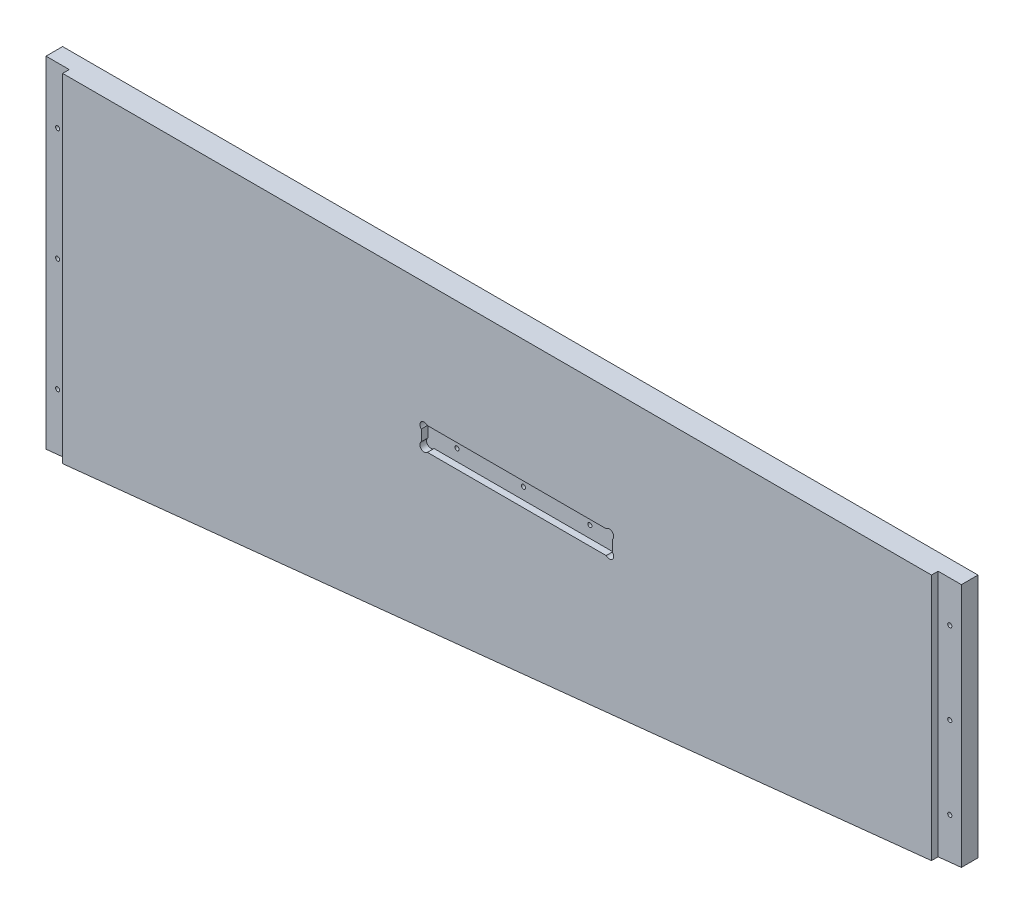
SolidWorks part; units mm, degrees
material "Pine"
ref_plane "Front Plane" through (0, 0, 0) normal (0, 0, 1) x (1, 0, 0)
ref_plane "Top Plane" through (0, 0, 0) normal (0, 1, 0) x (1, 0, 0)
ref_plane "Right Plane" through (0, 0, 0) normal (1, 0, 0) x (0, 0, -1)
sketch "Sketch1" plane through (0, 0, 0) normal (0, 0, 1) x (1, 0, 0)
  line L0 (-163.9887, -5335.905) -> (-163.9887, -5432.425)
  line L1 (-102.87, -5350.891) -> (-33.02, -5350.891)
  line L2 (-111.8235, -5341.9375) -> (-111.8235, -5334)
  line L3 (-24.0665, -5341.9375) -> (-24.0665, -5334)
  line L4 (-298.9262, -5332.73) -> (-167.1637, -5332.73)
  line L5 (-167.1637, -5435.6) -> (-298.9262, -5435.6)
  line L6 (-302.1012, -5432.425) -> (-302.1012, -5335.905)
  line L7 (-107.6325, -5329.809) -> (-28.2575, -5329.809)
  line L8 (174.9425, -5308.6) -> (174.9425, -5581.65)
  line L9 (449.2625, -5413.1661) -> (449.2625, -5421.9659)
  line L10 (595.3125, -5421.9659) -> (595.3125, -5413.1661)
  line L11 (839.47, -5509.5521) -> (839.47, -5307.6729)
  line L12 (839.47, -5307.6729) -> (863.6, -5307.6729)
  line L13 (839.47, -5509.5521) -> (863.6, -5509.5521)
  line L14 (863.6, -5509.5521) -> (863.6, -5307.6729)
  line L15 (-354.2665, -5341.9375) -> (-354.2665, -5334)
  line L16 (-100.8856, -5889.625) -> (-50.0856, -5889.625)
  line L17 (-104.0606, -5969) -> (-104.0606, -5892.8)
  line L18 (-46.9106, -5892.8) -> (-46.9106, -5969)
  line L19 (-50.0856, -5972.175) -> (-100.8856, -5972.175)
  line L20 (-100.8856, -5848.35) -> (-50.0856, -5848.35)
  line L21 (857.25, -5502.275) -> (157.1625, -5575.3)
  line L22 (857.25, -5314.95) -> (857.25, -5502.275)
  line L23 (157.1625, -5314.95) -> (157.1625, -5575.3)
  line L24 (857.25, -5314.95) -> (157.1625, -5314.95)
  line L25 (150.8125, -5308.6) -> (174.9425, -5308.6)
  line L26 (174.9425, -5581.65) -> (150.8125, -5581.65)
  line L27 (137.16, -5314.95) -> (137.16, -5502.275)
  line L28 (150.8125, -5581.65) -> (150.8125, -5308.6)
  line L29 (590.8224, -5408.676) -> (453.7526, -5408.676)
  line L30 (453.7526, -5426.456) -> (590.8224, -5426.456)
  line L31 (137.16, -6013.45) -> (137.16, -5867.4)
  line L32 (150.8125, -5746.75) -> (150.8125, -6019.8)
  line L33 (143.51, -5639.9938) -> (143.51, -5654.294)
  line L34 (590.8224, -5919.724) -> (453.7526, -5919.724)
  line L35 (453.7526, -5901.944) -> (590.8224, -5901.944)
  line L36 (449.2625, -5915.2339) -> (449.2625, -5906.4341)
  line L37 (174.9425, -6019.8) -> (174.9425, -5746.75)
  line L38 (595.3125, -5906.4341) -> (595.3125, -5915.2339)
  line L39 (839.47, -5818.8479) -> (839.47, -6020.7271)
  line L40 (839.47, -5818.8479) -> (863.6, -5818.8479)
  line L41 (863.6, -5818.8479) -> (863.6, -6020.7271)
  line L42 (839.47, -6020.7271) -> (863.6, -6020.7271)
  line L43 (-155.8782, -5867.4) -> (-603.25, -5867.4)
  line L44 (-433.07, -5350.891) -> (-363.22, -5350.891)
  line L45 (-437.8325, -5329.809) -> (-358.4575, -5329.809)
  line L46 (889, -6045.2) -> (-635, -6045.2)
  line L47 (-635, -5283.2) -> (889, -5283.2)
  line L48 (-635, -6045.2) -> (-635, -5283.2)
  line L49 (889, -5283.2) -> (889, -6045.2)
  line L50 (137.16, -5502.275) -> (-603.25, -5502.275)
  line L51 (-603.25, -5314.95) -> (137.16, -5314.95)
  line L52 (143.51, -5654.294) -> (-609.6, -5654.294)
  line L53 (-609.6, -5639.9938) -> (143.51, -5639.9938)
  line L54 (137.16, -5536.0062) -> (-603.25, -5536.0062)
  line L55 (-603.25, -5794.375) -> (137.16, -5794.375)
  line L56 (-603.25, -6013.45) -> (137.16, -6013.45)
  line L57 (-603.25, -5536.0062) -> (-603.25, -5794.375)
  line L58 (137.16, -5794.375) -> (137.16, -5536.0062)
  line L59 (-609.6, -5654.294) -> (-609.6, -5639.9938)
  line L60 (-603.25, -5867.4) -> (-603.25, -6013.45)
  line L61 (-603.25, -5314.95) -> (-603.25, -5502.275)
  line L62 (-442.0235, -5341.9375) -> (-442.0235, -5334)
  line L63 (857.25, -5826.125) -> (157.1625, -5753.1)
  line L64 (857.25, -6013.45) -> (857.25, -5826.125)
  line L65 (157.1625, -6013.45) -> (157.1625, -5753.1)
  line L66 (857.25, -6013.45) -> (157.1625, -6013.45)
  line L67 (174.9425, -5746.75) -> (150.8125, -5746.75)
  line L68 (150.8125, -6019.8) -> (174.9425, -6019.8)
  line L69 (137.16, -5867.4) -> (4.907, -5867.4)
  circle A0 centre (-36.195, -5484.0124) radius 1.5875
  arc A1 (-298.9262, -5332.73) -> (-302.1012, -5335.905) centre (-298.9262, -5335.905) ccw
  arc A2 (-302.1012, -5432.425) -> (-298.9262, -5435.6) centre (-298.9262, -5432.425) ccw
  arc A3 (-163.9887, -5335.905) -> (-167.1637, -5332.73) centre (-167.1637, -5335.905) ccw
  arc A4 (-167.1637, -5435.6) -> (-163.9887, -5432.425) centre (-167.1637, -5432.425) ccw
  arc A5 (-111.8235, -5341.9375) -> (-102.87, -5350.891) centre (-102.87, -5341.9375) ccw
  arc A6 (-107.6325, -5329.809) -> (-111.8235, -5334) centre (-107.6325, -5334) ccw
  circle A7 centre (166.0525, -5444.6613) radius 1.5875
  circle A8 centre (166.0525, -5358.1871) radius 1.5875
  circle A9 centre (471.4875, -5417.566) radius 1.5875
  arc A10 (453.7526, -5408.676) -> (449.2625, -5413.1661) centre (451.5076, -5410.9211) ccw
  arc A11 (449.2625, -5421.9659) -> (453.7526, -5426.456) centre (451.5076, -5424.2109) ccw
  circle A12 centre (522.2875, -5417.566) radius 1.5875
  circle A13 centre (573.0875, -5417.566) radius 1.5875
  arc A14 (590.8224, -5426.456) -> (595.3125, -5421.9659) centre (593.0674, -5424.2109) ccw
  arc A15 (595.3125, -5413.1661) -> (590.8224, -5408.676) centre (593.0674, -5410.9211) ccw
  circle A16 centre (848.36, -5471.8269) radius 1.5875
  circle A17 centre (848.36, -5409.0762) radius 1.5875
  circle A18 centre (848.36, -5346.3254) radius 1.5875
  arc A19 (-363.22, -5350.891) -> (-354.2665, -5341.9375) centre (-363.22, -5341.9375) ccw
  arc A20 (-354.2665, -5334) -> (-358.4575, -5329.809) centre (-358.4575, -5334) ccw
  arc A21 (-24.0665, -5334) -> (-28.2575, -5329.809) centre (-28.2575, -5334) ccw
  arc A22 (-33.02, -5350.891) -> (-24.0665, -5341.9375) centre (-33.02, -5341.9375) ccw
  circle A23 centre (-86.995, -5484.0124) radius 1.5875
  circle A24 centre (-333.4544, -5894.07) radius 2.54
  circle A25 centre (-333.4544, -5994.4) radius 2.54
  arc A26 (-104.0606, -5969) -> (-100.8856, -5972.175) centre (-100.8856, -5969) ccw
  arc A27 (-50.0856, -5972.175) -> (-46.9106, -5969) centre (-50.0856, -5969) ccw
  arc A28 (-100.8856, -5848.35) -> (-128.3819, -5857.875) centre (-100.8856, -5892.8) ccw
  arc A29 (-155.8782, -5867.4) -> (-128.3819, -5857.875) centre (-155.8782, -5822.95) ccw
  arc A30 (-22.5893, -5857.875) -> (-50.0856, -5848.35) centre (-50.0856, -5892.8) ccw
  circle A31 centre (-132.6356, -5894.07) radius 2.54
  circle A32 centre (-132.6356, -5994.4) radius 2.54
  arc A33 (-46.9106, -5892.8) -> (-50.0856, -5889.625) centre (-50.0856, -5892.8) ccw
  arc A34 (-100.8856, -5889.625) -> (-104.0606, -5892.8) centre (-100.8856, -5892.8) ccw
  arc A35 (-22.5893, -5857.875) -> (4.907, -5867.4) centre (4.907, -5822.95) ccw
  circle A36 centre (166.0525, -5531.1356) radius 1.5875
  arc A37 (449.2625, -5915.2339) -> (453.7526, -5919.724) centre (451.5076, -5917.4789) ccw
  arc A38 (453.7526, -5901.944) -> (449.2625, -5906.4341) centre (451.5076, -5904.1891) ccw
  circle A39 centre (166.0525, -5797.2644) radius 1.5875
  circle A40 centre (166.0525, -5883.7387) radius 1.5875
  circle A41 centre (166.0525, -5970.2129) radius 1.5875
  circle A42 centre (471.4875, -5910.834) radius 1.5875
  circle A43 centre (522.2875, -5910.834) radius 1.5875
  circle A44 centre (573.0875, -5910.834) radius 1.5875
  arc A45 (595.3125, -5906.4341) -> (590.8224, -5901.944) centre (593.0674, -5904.1891) ccw
  arc A46 (590.8224, -5919.724) -> (595.3125, -5915.2339) centre (593.0674, -5917.4789) ccw
  circle A47 centre (848.36, -5919.3238) radius 1.5875
  circle A48 centre (848.36, -5982.0746) radius 1.5875
  circle A49 centre (848.36, -5856.5731) radius 1.5875
  arc A50 (-437.8325, -5329.809) -> (-442.0235, -5334) centre (-437.8325, -5334) ccw
  circle A51 centre (-429.895, -5484.0124) radius 1.5875
  arc A52 (-442.0235, -5341.9375) -> (-433.07, -5350.891) centre (-433.07, -5341.9375) ccw
  circle A53 centre (-379.095, -5484.0124) radius 1.5875
sketch "Sketch2" plane through (0, 0, 0) normal (0, 0, 1) x (1, 0, 0)
  line L0 (857.25, -5502.275) -> (857.25, -5314.95)
  line L1 (857.25, -5314.95) -> (157.1625, -5314.95)
  line L2 (157.1625, -5314.95) -> (157.1625, -5575.3)
  line L3 (157.1625, -5575.3) -> (857.25, -5502.275)
extrude "Extrude1" add sketch "Sketch2" against normal blind 17.78
sketch "Sketch3" plane through (0, 0, 0) normal (0, 0, 1) x (1, 0, 0)
  circle A0 centre (166.0525, -5531.1356) radius 1.5875
  circle A1 centre (166.0525, -5444.6613) radius 1.5875
  circle A2 centre (166.0525, -5358.1871) radius 1.5875
  circle A3 centre (848.36, -5471.8269) radius 1.5875
  circle A4 centre (848.36, -5409.0762) radius 1.5875
  circle A5 centre (848.36, -5346.3254) radius 1.5875
  circle A6 centre (573.0875, -5417.566) radius 1.5875
  circle A7 centre (522.2875, -5417.566) radius 1.5875
  circle A8 centre (471.4875, -5417.566) radius 1.5875
extrude "Cut-Extrude1" cut sketch "Sketch3" against normal up to surface (17.78 mm away) up to face at (507.2062, -5426.8687, -17.78)
sketch "Sketch4" plane through (0, 0, 0) normal (0, 0, 1) x (1, 0, 0)
  line L0 (157.1625, -5314.95) -> (157.1625, -5575.3)
  line L1 (157.1625, -5575.3) -> (174.9425, -5575.3)
  line L2 (174.9425, -5308.6) -> (174.9425, -5581.65) construction
  line L3 (174.9425, -5575.3) -> (174.9425, -5314.95)
  line L4 (857.25, -5314.95) -> (157.1625, -5314.95) construction
  line L5 (174.9425, -5314.95) -> (157.1625, -5314.95)
  line L6 (857.25, -5314.95) -> (839.47, -5314.95)
  line L7 (839.47, -5509.5521) -> (839.47, -5307.6729) construction
  line L8 (839.47, -5314.95) -> (839.47, -5504.1296)
  line L9 (857.25, -5502.275) -> (157.1625, -5575.3) construction
  line L10 (839.47, -5504.1296) -> (857.25, -5504.1296)
  line L11 (857.25, -5504.1296) -> (857.25, -5314.95)
  line L12 (449.2625, -5426.456) -> (595.3125, -5426.456)
  line L13 (595.3125, -5408.676) -> (595.3125, -5426.456)
  line L14 (595.3125, -5408.676) -> (449.2625, -5408.676)
  line L15 (449.2625, -5408.676) -> (449.2625, -5426.456)
extrude "Cut-Extrude2" cut sketch "Sketch4" against normal blind 5.08
sketch "Sketch6" plane through (0, 0, 0) normal (0, 0, 1) x (1, 0, 0)
  line L0 (595.3125, -5426.456) -> (593.0674, -5424.2109) construction
  line L1 (595.3125, -5408.676) -> (593.0674, -5410.9211) construction
  line L2 (449.2625, -5426.456) -> (451.5076, -5424.2109) construction
  line L3 (449.2625, -5408.676) -> (451.5076, -5410.9211) construction
  circle A0 centre (451.5076, -5410.9211) radius 3.302
  circle A1 centre (451.5076, -5424.2109) radius 3.302
  circle A2 centre (593.0674, -5424.2109) radius 3.302
  circle A3 centre (593.0674, -5410.9211) radius 3.302
extrude "Cut-Extrude3" cut sketch "Sketch6" against normal up to surface (5.08 mm away) up to face at (523.875, -5417.566, -5.08)
